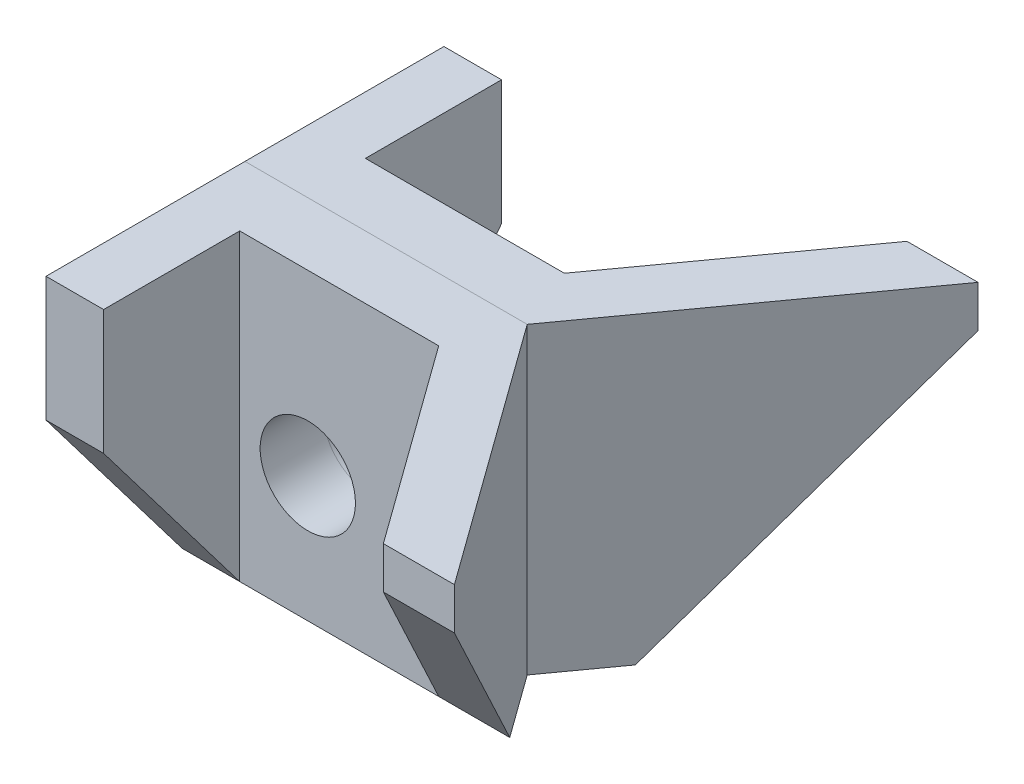
SolidWorks part; units mm, degrees
material "6061-T6 (SS)"
ref_plane "Front Plane" through (0, 0, 0) normal (0, 0, 1) x (1, 0, 0)
ref_plane "Top Plane" through (0, 0, 0) normal (0, 1, 0) x (1, 0, 0)
ref_plane "Right Plane" through (0, 0, 0) normal (1, 0, 0) x (0, 0, -1)
sketch "Sketch1" plane through (0, 0, 0) normal (0, 0, 1) x (1, 0, 0)
  line L0 (-12, -12) -> (-12, 17)
  line L1 (33, -12) -> (33, 12)
  line L2 (33, 17) -> (-12, 17)
  line L3 (33, 17) -> (33, 12)
  line L4 (0, 0) -> (0, -12) construction
  line L5 (0, -12) -> (-12, -12)
  line L6 (0, -12) -> (33, -12)
  circle A0 centre (0, 0) radius 12 construction
  circle A3 centre (0, 0) radius 4.55
  dimension "D1" = 24
  dimension "D2" = 29
  dimension "D5" = 9.1
  dimension "D3" = 45
  dimension "D4" = 5
extrude "Boss-Extrude1" add sketch "Sketch1" against normal blind 25
sketch "Sketch2" plane through (0, 17, 0) normal (0, 1, 0) x (1, 0, 0)
  line L0 (-6.5, 25) -> (-6.5, 6)
  line L1 (33, 25) -> (-12, 25) construction
  line L3 (-6.5, 6) -> (12.5, 6)
  line L6 (-12, 19) -> (-6.5, 19)
  line L9 (-12, 25) -> (-12, 0) construction
  line L11 (12.5, 6) -> (26.2165, 25)
  line L12 (33, 25) -> (14.9519, 0)
  line L13 (33, 25) -> (33, 0) construction
  line L14 (-15.95, 0) -> (15.95, 0) construction
  line L15 (33, 25) -> (-12, 25) construction
  line M9 (-12, 0) -> (33, 0)
  line M10 (33, 0) -> (33, 25)
  line M11 (33, 25) -> (-12, 25)
  line M12 (-12, 25) -> (-12, 0)
  dimension "D5" = 5.5
  dimension "D1" = 6
  dimension "D2" = 6
  dimension "D3" = 19
  dimension "D4" = 5.5
extrude "Cut-Extrude1" cut sketch "Sketch2" against normal through all contours L12 M10 M9 | L3 L11 L0 M11 | L6 L0 M12 M11
sketch "Sketch4" plane through (-6.5, 0, 0) normal (1, 0, 0) x (0, 0, -1)
  line L0 (6, -12) -> (25, 13)
  line L12 (25, 17) -> (6, 17)
  line L14 (25, -12) -> (25, 17)
  line L15 (6, -12) -> (25, -12)
  line L16 (6, 17) -> (6, -12)
  line L17 (25, 17) -> (6, 17)
  line L18 (25, -12) -> (25, 17)
  line L19 (6, -12) -> (25, -12)
  line L20 (6, 17) -> (6, -12)
  line M7 (6, -12) -> (19, -12)
  line M15 (19, -12) -> (19, 17)
  dimension "D2" = 4
  dimension "D1" = 0
extrude "Cut-Extrude3" cut sketch "Sketch4" against normal up to surface and the other way up to surface contours L19 L18 L0 M15 | L0 M7 M15 up to face at (-12, 2.5, -9.5) other way up to face at (23.976, 2.5, -12.5)
mirror "Mirror3" about plane through (0, 0, 0) normal (0, 0, 1) of bodies 110 106
